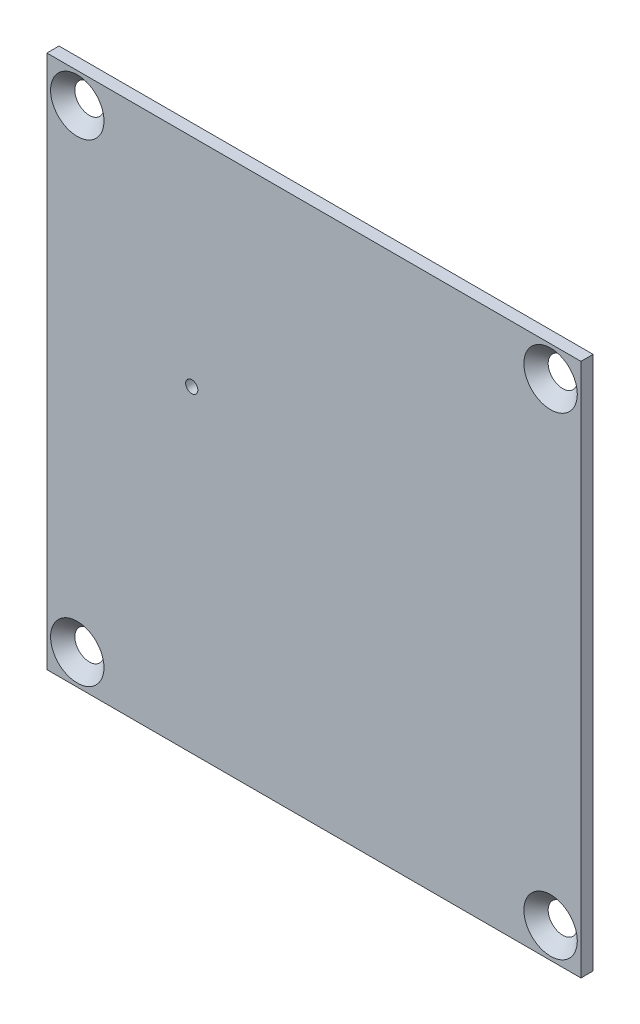
SolidWorks part; units mm, degrees
ref_plane "Plan de face" through (0, 0, 0) normal (1, 0, 0) x (0, 1, 0)
ref_plane "Plan de dessus" through (0, 0, 0) normal (0, 0, 1) x (0, 1, 0)
ref_plane "Plan de droite" through (0, 0, 0) normal (0, 1, 0) x (-1, 0, 0)
sketch "Esquisse3" plane through (0, 0, 0) normal (0, 0, 1) x (0, 1, 0)
  line L1 (-22, -22) -> (22, -22)
  line L2 (-22, -22) -> (-22, 22)
  line L3 (-22, 22) -> (22, 22)
  line L4 (22, -22) -> (22, 22)
  line L5 (-22, -22) -> (22, 22) construction
  line L6 (-22, 22) -> (22, -22) construction
  point P0 (0, 0)
extrude "Boss.-Extru.1" add sketch "Esquisse3" along normal blind 1
sketch "Sketch_Holes" plane through (0, 0, 1) normal (0, 0, 1) x (1, 0, 0)
  circle A0 centre (-10.0677, 4.1602) radius 0.5
extrude "Cut_Extrude_Holes" cut sketch "Sketch_Holes" against normal through all
hole_wizard "Fraisage pour vis à tête fraisée M21" positions "Esquisse4" profile "Esquisse5" countersink size "M2" standard "Ansi Metric" end condition through all
sketch "Esquisse4" plane through (0, 0, 1) normal (0, 0, 1) x (1, 0, 0)
  line L4 (-22, 22) -> (-22, -22) construction
  line L5 (22, 22) -> (-22, 22) construction
  line L6 (22, -22) -> (22, 22) construction
  line L7 (-22, -22) -> (22, -22) construction
  point P2 (19.5, -19.5)
  point P19 (-19.5, -19.5)
  point P21 (-19.5, 19.5)
  point P23 (19.5, 19.5)
  dimension "D3" = 41.5
  dimension "D4" = 41.5
sketch "Esquisse5" plane through (19.5, -19.5, 1) normal (1, 0, 0) x (0, -1, 0)
  line L0 (0, 0) -> (0, 2)
  line L1 (0, 2) -> (1.2, 2)
  line L2 (1.2, 2) -> (1.2, 1)
  line L3 (1.2, 1) -> (2.2, 0)
  line L5 (2.2, 0) -> (0, 0)
  line L6 (-1.2, 1) -> (-2.2, 0) construction
  line L11 (0, -6.35) -> (0, 107.95) construction
  dimension "Diamètre du perçage jusqu'au prochain" = 2.4
  dimension "Profondeur du perçage jusqu'au prochain" = 1
  dimension "Diamètre du fraisage entrant" = 4.4
  dimension "Angle du fraisage entrant" = 90
equation "\"Plaque_L\" =\"Cavite_L\"+\"Cavite_E\"'longueur plaque"
equation "\"Plaque_H\" = \"Cavite_L\"+\"Cavite_E\"'largeur plaque"
equation "\"Plaque_E\"= 1mm'épaisseur plaque"
equation "\"Trou_R\"= 1.2mm'rayon perforation base"
equation "\"Trou_dx\"= 4mm'distance entre trou sur x"
equation "\"Trou-dy\"= 4mm'distance entre trou sur y"
equation "\"Cavite_H\" = 18mm'hauteur cavité"
equation "\"Cavite_L\" =\"Cavite_largeur\"+\"Cavite_E\"'longueur cavité"
equation "\"Cavite_E\"= 3mm'épaisseur cavité"
equation "\"Offset_Z\"= 0mm"
equation "\"D1@Esquisse3\"=\"largeur_plaque_enveloppe\""
equation "\"D2@Esquisse3\"=\"largeur_plaque_enveloppe\""
equation "\"D1@Boss.-Extru.1\"=\"Plaque_E\""
equation "\"N_Plaque\" = 7"
equation "\"N_Cavite\"= 6"
equation "\"Cavite_largeur\"= 28mm'largeur cavité"
equation "\"Offset_cavite\" = \"Cavite_E\" / 2"
equation "\"Offset_hauteur_vis1\"= \"Cavite_E\""
equation "\"Offset_hauteur_vis2\"= \"Cavite_H\" - \"Cavite_E\""
equation "\"H_total\"=113mm'122-2*2"
equation "\"espace_vis\"=22.6mm'"
equation "\"Largeur_equerre_enveloppe\"=\"Cavite_L\"+\"Cavite_E\""
equation "\"Enveloppe_E\"=5mm"
equation "\"Offset_Enveloppe\" = \"Enveloppe_E\" / 2"
equation "\"Longueur_equerre_enveloppe\"=\"Cavite_L\"+\"Cavite_E\"+\"Enveloppe_E\""
equation "\"largeur_plaque_enveloppe\"=\"Longueur_equerre_enveloppe\"+\"Enveloppe_E\""
equation "\"D1@Esquisse4\"=\"largeur_plaque_enveloppe\"-\"Offset_Enveloppe\""
equation "\"D2@Esquisse4\"=\"largeur_plaque_enveloppe\"-\"Offset_Enveloppe\""
equation "\"D3@Esquisse4\"=\"largeur_plaque_enveloppe\"-\"Offset_Enveloppe\""
equation "\"D4@Esquisse4\"=\"largeur_plaque_enveloppe\"-\"Offset_Enveloppe\""
